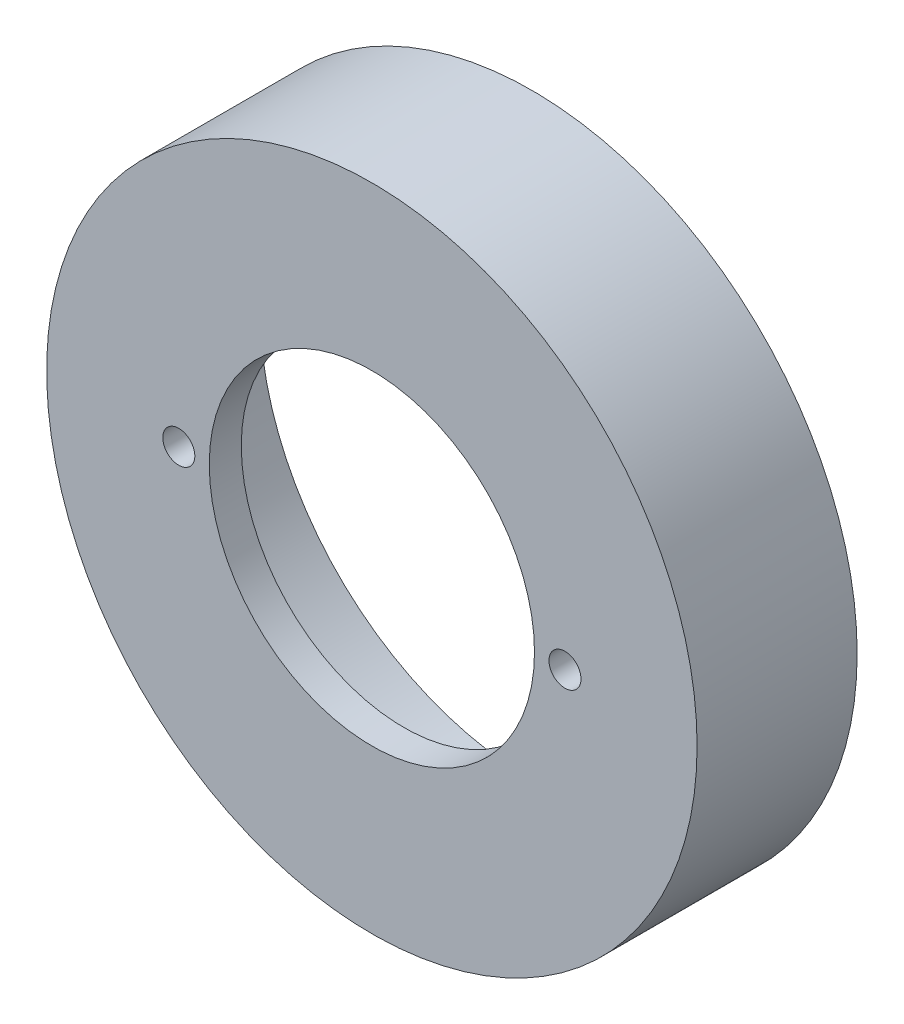
SolidWorks part; units mm, degrees
ref_plane "Plan de face" through (0, 0, 0) normal (0, 0, 1) x (1, 0, 0)
ref_plane "Plan de dessus" through (0, 0, 0) normal (0, 1, 0) x (1, 0, 0)
ref_plane "Plan de droite" through (0, 0, 0) normal (1, 0, 0) x (0, 0, -1)
sketch "Esquisse1" plane through (0, 0, 0) normal (0, 0, 1) x (1, 0, 0)
  circle A0 centre (0, 0) radius 50.8
  dimension "D1" = 101.6
extrude "Boss.-Extru.1" add sketch "Esquisse1" along normal blind 25
sketch "Esquisse2" plane through (0, 0, 25) normal (0, 0, 1) x (1, 0, 0)
  circle A0 centre (0, 0) radius 25.4
  dimension "D1" = 50.8
extrude "Enlèv. mat.-Extru.1" cut sketch "Esquisse2" against normal through all
sketch "Esquisse3" plane through (0, 0, 0) normal (0, 0, -1) x (-1, 0, 0)
  circle A0 centre (0, 0) radius 42.5
  dimension "D1" = 85
extrude "Enlèv. mat.-Extru.2" cut sketch "Esquisse3" against normal offset from surface (20 mm away) 5 up to face at (25.4, 0, 25)
sketch "Esquisse4" plane through (0, 0, 20) normal (0, 0, -1) x (-1, 0, 0)
  line L0 (0, 0) -> (-30.16, 0) construction
  line L1 (13.75, 0) -> (-13.75, 0) construction
  circle A0 centre (-30.16, 0) radius 2.5
  circle A1 centre (30.16, 0) radius 2.5
  point P10 (0, 0)
  dimension "D2" = 5
  dimension "D1" = 30.16
  dimension "D3" = 2
extrude "Enlèv. mat.-Extru.3" cut sketch "Esquisse4" against normal through all
sketch "Esquisse5" plane through (0, 0, 0) normal (0, 0, -1) x (-1, 0, 0)
  line L0 (0, 13.75) -> (0, -13.75) construction
  circle A0 centre (0, 46.6476) radius 2
  circle A2 centre (0, -47.3524) radius 2
  point P14 (0, -0.3524)
  dimension "D1" = 4
  dimension "D3" = 47
  dimension "D2" = 2
extrude "Enlèv. mat.-Extru.4" cut sketch "Esquisse5" against normal blind 7.5
